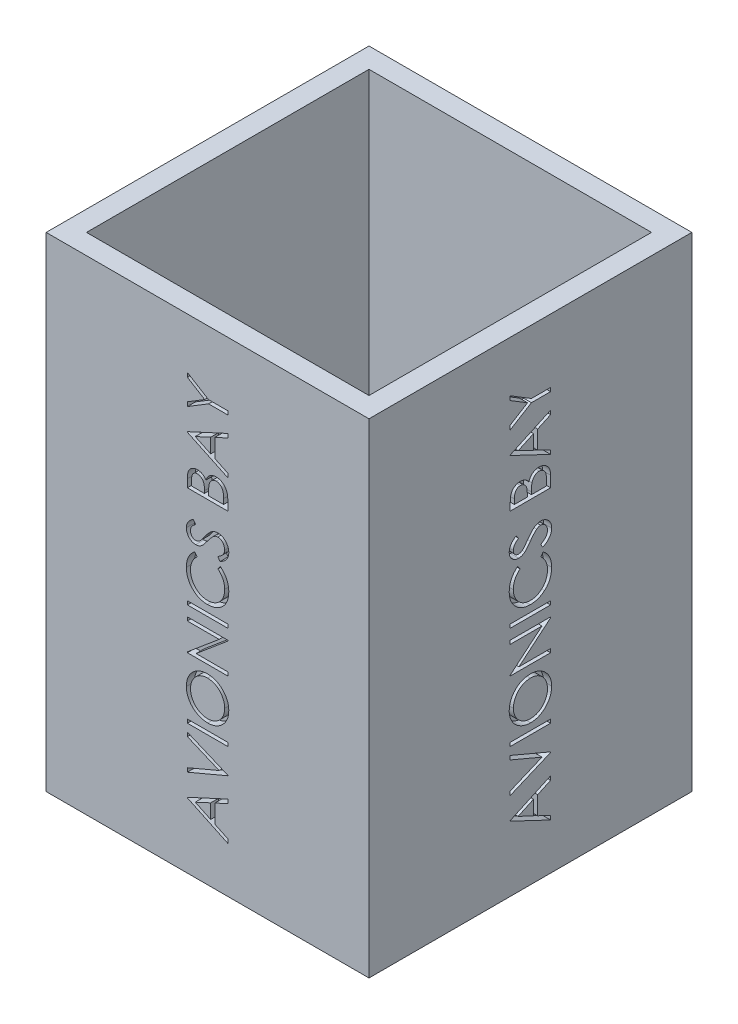
SolidWorks part; units mm, degrees
material "PVC Rigid"
ref_plane "Front Plane" through (0, 0, 0) normal (0, 0, 1) x (1, 0, 0)
ref_plane "Top Plane" through (0, 0, 0) normal (0, 1, 0) x (1, 0, 0)
ref_plane "Right Plane" through (0, 0, 0) normal (1, 0, 0) x (0, 0, -1)
sketch "Sketch1" plane through (0, 0, 0) normal (0, 1, 0) x (1, 0, 0)
  line L1 (-50.8, -50.8) -> (50.8, -50.8)
  line L2 (-50.8, -50.8) -> (-50.8, 50.8)
  line L3 (-50.8, 50.8) -> (50.8, 50.8)
  line L4 (50.8, -50.8) -> (50.8, 50.8)
  line L5 (-50.8, -50.8) -> (50.8, 50.8) construction
  line L6 (-50.8, 50.8) -> (50.8, -50.8) construction
  line L7 (-44.45, -44.45) -> (44.45, -44.45)
  line L8 (-44.45, -44.45) -> (-44.45, 44.45)
  line L9 (-44.45, 44.45) -> (44.45, 44.45)
  line L10 (44.45, -44.45) -> (44.45, 44.45)
  line L11 (-44.45, -44.45) -> (44.45, 44.45) construction
  line L12 (-44.45, 44.45) -> (44.45, -44.45) construction
  point P0 (0, 0)
  point P6 (0, 0)
  dimension "D1" = 101.6
  dimension "D2" = 101.6
  dimension "D3" = 88.9
extrude "Boss-Extrude1" add sketch "Sketch1" along normal blind 152.4
sketch "Sketch6" plane through (-50.8, 0, 0) normal (-1, 0, 0) x (0, 0, 1)
  line L0 (6.35, 0) -> (6.35, 152.4) construction
  line L1 (-50.8, 0) -> (50.8, 0) construction
  line L2 (-50.8, 152.4) -> (50.8, 152.4) construction
  line L3 (-50.8, 152.4) -> (-50.8, 0) construction
  text T0 "AVIONICS BAY" font "Century Gothic" height in points 48
  dimension "D1" = 57.15
extrude "Cut-Extrude1" cut sketch "Sketch6" against normal blind 2.54
sketch "Sketch7" plane through (0, 0, 0) normal (0, 0, 1) x (1, 0, 0)
  line L0 (0, 0) -> (0, 152.4) construction
  line L1 (-50.8, 152.4) -> (50.8, 152.4) construction
pattern_circular "CirPattern1" count 4 over 360 about axis through (0, 0, 0) along (0, 1, 0) of "Cut-Extrude1"
